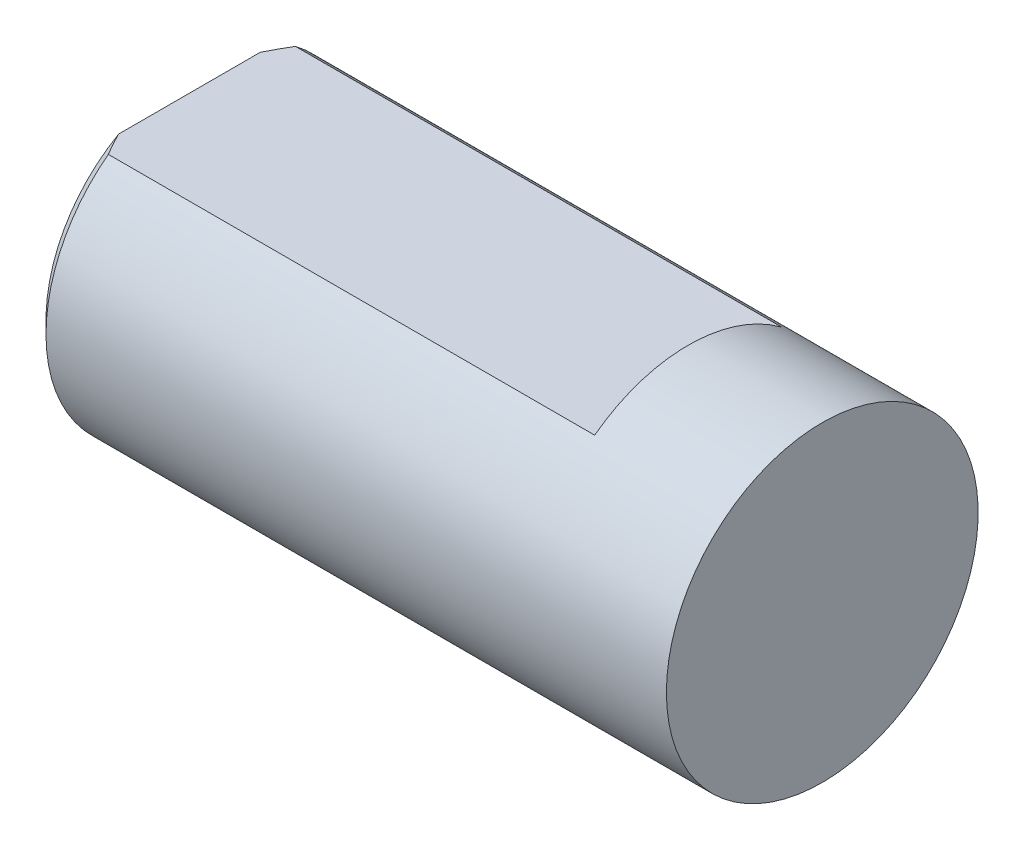
SolidWorks part; units mm, degrees
ref_plane "Plan de face" through (0, 0, 0) normal (0, 0, 1) x (1, 0, 0)
ref_plane "Plan de dessus" through (0, 0, 0) normal (0, 1, 0) x (1, 0, 0)
ref_plane "Plan de droite" through (0, 0, 0) normal (1, 0, 0) x (0, 0, -1)
sketch "Esquisse1" plane through (0, 0, 0) normal (0, 0, 1) x (1, 0, 0)
  line L0 (0, 0) -> (29.185, 0) construction
  line L1 (0, 0) -> (0, 2.5)
  line L4 (0, 2.5) -> (-10.15, 2.5)
  line L5 (-10.15, 2.5) -> (-10.15, 0)
  line L6 (-10.15, 0) -> (0, 0)
  dimension "D1" = 5
  dimension "D2" = 10.15
revolve "Révolution1" add sketch "Esquisse1" angle 360 about L0
sketch "Esquisse2" plane through (-10.15, 0, 0) normal (-1, 0, 0) x (0, 0, 1)
  line L0 (-1.5, 2) -> (0, 2)
  line L1 (0, 2) -> (0, 0) construction
  line L2 (0, 2) -> (1.5, 2)
  line L3 (0, 0) -> (0, -2.5) construction
  circle A0 centre (0, 0) radius 2.5 construction
  arc A1 (1.5, 2) -> (-1.5, 2) centre (0, 0) ccw
  dimension "D1" = 4.5
extrude "Enlèv. mat.-Extru.1" cut sketch "Esquisse2" against normal blind 8
chamfer "Chanfrein1" distance 0.2 angle 45 1 edges at (-10.15, -2.5, 0)
